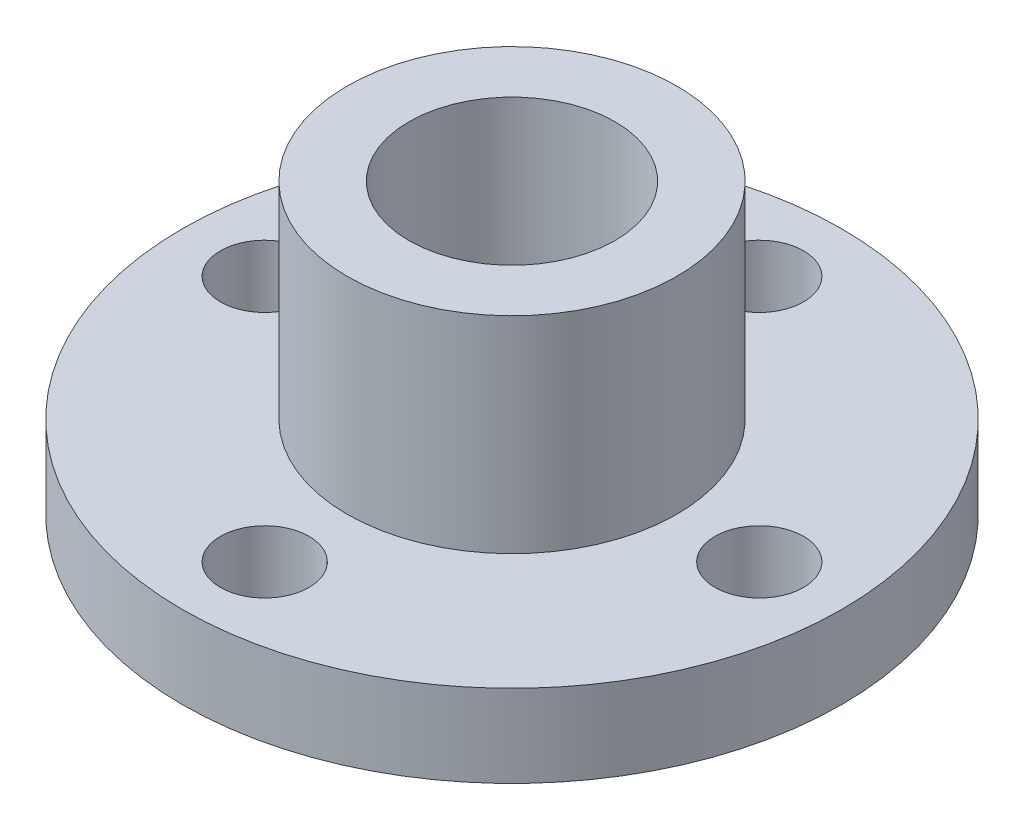
SolidWorks part; units mm, degrees
ref_plane "Front Plane" through (0, 0, 0) normal (0, 0, 1) x (1, 0, 0)
ref_plane "Top Plane" through (0, 0, 0) normal (0, 1, 0) x (1, 0, 0)
ref_plane "Right Plane" through (0, 0, 0) normal (1, 0, 0) x (0, 0, -1)
sketch "Sketch1" plane through (0, 0, 0) normal (1, 0, 0) x (0, 0, -1)
  line L2 (8, 0) -> (8, -10)
  line L3 (8, -10) -> (16, -10)
  line L4 (16, -10) -> (16, -14)
  line L5 (16, -14) -> (5, -14)
  line L8 (0, 0) -> (0, -22.8342) construction
  line L9 (5, 0) -> (5, -14)
  line L10 (5, 0) -> (8, 0)
  point P0 (6.5, 0)
  dimension "D1" = 16
  dimension "D2" = 8
  dimension "D3" = 10
  dimension "D4" = 4
  dimension "D5" = 5
  dimension "D6" = 14
revolve "Revolve4" add sketch "Sketch1" angle 360 about L8
sketch "Sketch2" plane through (0, -10, 0) normal (0, 1, 0) x (1, 0, 0)
  circle A0 centre (-12, 0) radius 2.15
  circle A1 centre (0, 0) radius 12 construction
  dimension "D1" = 24
  dimension "D2" = 4.3
extrude "Cut-Extrude1" cut sketch "Sketch2" against normal through all contours A0
pattern_circular "CirPattern1" count 4 over 360 about axis through (0, 0, 0) along (0, 1, 0) of "Cut-Extrude1"
equation "\"D1@Sketch2\"=(32+16)/2"
